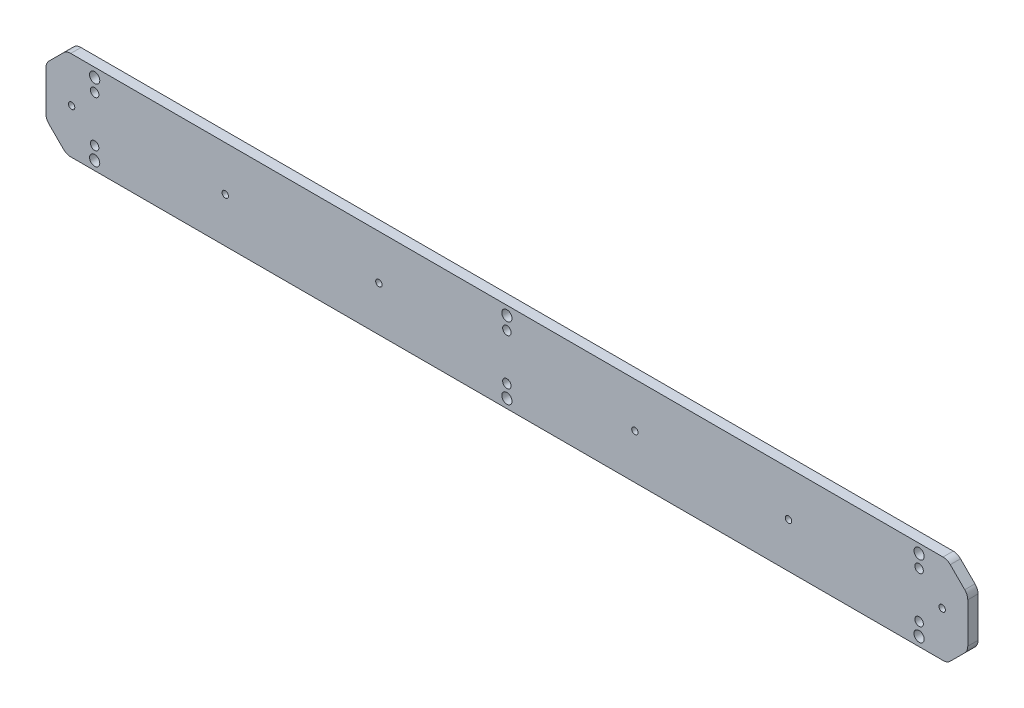
SolidWorks part; units mm, degrees
material "acero"
ref_plane "Alzado" through (0, 0, 0) normal (0, 0, 1) x (1, 0, 0)
ref_plane "Planta" through (0, 0, 0) normal (0, 1, 0) x (1, 0, 0)
ref_plane "Vista lateral" through (0, 0, 0) normal (1, 0, 0) x (0, 0, -1)
sketch "Croquis1" plane through (0, 0, 0) normal (0, 0, 1) x (1, 0, 0)
  line L0 (0, 14) -> (0, -14) construction
  line L1 (-180, -17.5) -> (180, -17.5)
  line L2 (-180, -17.5) -> (-180, 17.5)
  line L3 (-180, 17.5) -> (180, 17.5)
  line L4 (180, -17.5) -> (180, 17.5)
  line L5 (-180, -17.5) -> (180, 17.5) construction
  line L6 (-180, 17.5) -> (180, -17.5) construction
  circle A0 centre (0, 14) radius 1.6 construction
  circle A1 centre (0, -14) radius 1.6 construction
  point P0 (0, 0)
  dimension "D3" = 28
  dimension "D4" = 3.2
  dimension "D1" = 360
  dimension "D2" = 35
extrude "Saliente-Extruir1" add sketch "Croquis1" along normal blind 4
sketch "Croquis2" plane through (0, 0, 4) normal (0, 0, 1) x (1, 0, 0)
  line L0 (0, 0) -> (-161, 0) construction
  line L1 (0, 0) -> (161, 0) construction
  line L2 (161, 14) -> (161, -14) construction
  line L3 (-161, 14) -> (-161, -14) construction
  line L4 (0, 14) -> (0, -14) construction
  circle A0 centre (0, 14) radius 2
  circle A1 centre (0, -14) radius 2
  circle A2 centre (161, 14) radius 2
  circle A3 centre (161, -14) radius 2
  circle A4 centre (-161, 14) radius 2
  circle A5 centre (-161, -14) radius 2
  dimension "D1" = 4
  dimension "D2" = 161
  dimension "D4" = 28
extrude "Cortar-Extruir1" cut sketch "Croquis2" against normal blind 5
sketch "Croquis4" plane through (0, 0, 4) normal (0, 0, 1) x (1, 0, 0)
  line L0 (-161, 0) -> (0, 0) construction
  line L1 (0, 0) -> (161, 0) construction
  line L2 (161, 9) -> (161, -9) construction
  line L3 (0, 9) -> (0, -9) construction
  line L4 (-161, 9) -> (-161, -9) construction
  dimension "D1" = 161
  dimension "D2" = 18
hole_wizard "Perforador para roscar para macho de roscar para M41" positions "Croquis3D2" profile "Croquis5" hole size "M4" standard "Din" end condition through all
sketch3d "Croquis3D2"
  point P0 (-161, 9, 4)
  point P3 (-161, -9, 4)
  point P6 (0, 9, 4)
  point P9 (0, -9, 4)
  point P12 (161, 9, 4)
  point P15 (161, -9, 4)
sketch "Croquis5" plane through (-161, 9, 4) normal (1, 0, 0) x (0, -1, 0)
  line L0 (0, 0) -> (0, 4)
  line L1 (0, 4) -> (1.65, 4)
  line L2 (1.65, 4) -> (1.65, 0)
  line L5 (1.65, 0) -> (0, 0)
  line L11 (0, -6.35) -> (0, 107.95) construction
  dimension "Diámetro de taladro hasta el siguiente" = 3.3
  dimension "Profundidad de taladro hasta el siguiente" = 4
cosmetic thread "Rosca cosmética1" parameters "D2"=4
cosmetic thread "Rosca cosmética2" parameters "D2"=4
cosmetic thread "Rosca cosmética3" parameters "D2"=4
cosmetic thread "Rosca cosmética4" parameters "D2"=4
cosmetic thread "Rosca cosmética5" parameters "D2"=4
cosmetic thread "Rosca cosmética6" parameters "D2"=4
sketch "Croquis6" plane through (0, 0, 4) normal (0, 0, 1) x (1, 0, 0)
  line L0 (-10, 0) -> (-170, 0) construction
  line L1 (-161, 0) -> (0, 0) construction
  line L2 (-10, 0) -> (170, 0) construction
  line L3 (-10, 0) -> (-50, 0) construction
  line L4 (-10, 0) -> (50, 0) construction
  line L5 (-50, 0) -> (-110, 0) construction
  line L6 (50, 0) -> (110, 0) construction
  dimension "D1" = 10
  dimension "D2" = 180
  dimension "D3" = 160
  dimension "D4" = 40
  dimension "D5" = 60
  dimension "D6" = 60
  dimension "D7" = 60
hole_wizard "Taladro roscado M31" positions "Croquis7" profile "Croquis9" tap size "M3" standard "ISO" end condition through all
sketch "Croquis7" plane through (0, 0, 4) normal (0, 0, 1) x (1, 0, 0)
  point P0 (-170, 0)
  point P5 (-110, 0)
  point P8 (-50, 0)
  point P11 (50, 0)
  point P14 (110, 0)
  point P17 (170, 0)
sketch "Croquis9" plane through (-170, 0, 4) normal (1, 0, 0) x (0, -1, 0)
  line L0 (0, 0) -> (0, 4)
  line L1 (0, 4) -> (1.25, 4)
  line L2 (1.25, 4) -> (1.25, 0)
  line L5 (1.25, 0) -> (0, 0)
  line L11 (0, -6.35) -> (0, 107.95) construction
  dimension "Diámetro de perforador para roscar hasta el siguiente" = 2.5
  dimension "Profundidad de perforador para roscar hasta el siguiente" = 4
cosmetic thread "Rosca de taladro1" parameters "D2"=3
cosmetic thread "Rosca de taladro2" parameters "D2"=3
cosmetic thread "Rosca de taladro3" parameters "D2"=3
cosmetic thread "Rosca de taladro4" parameters "D2"=3
cosmetic thread "Rosca de taladro5" parameters "D2"=3
cosmetic thread "Rosca de taladro6" parameters "D2"=3
chamfer "Chaflán1" distance 8 angle 45 4 edges at (180, -17.5, 2) (180, 17.5, 2) (-180, -17.5, 2) (-180, 17.5, 2)
fillet "Redondeo2" radius 4 8 edges at (-172, -17.5, 2) (-180, -9.5, 2) (-180, 9.5, 2) (-172, 17.5, 2) (172, -17.5, 2) (180, -9.5, 2) (180, 9.5, 2) (172, 17.5, 2)
